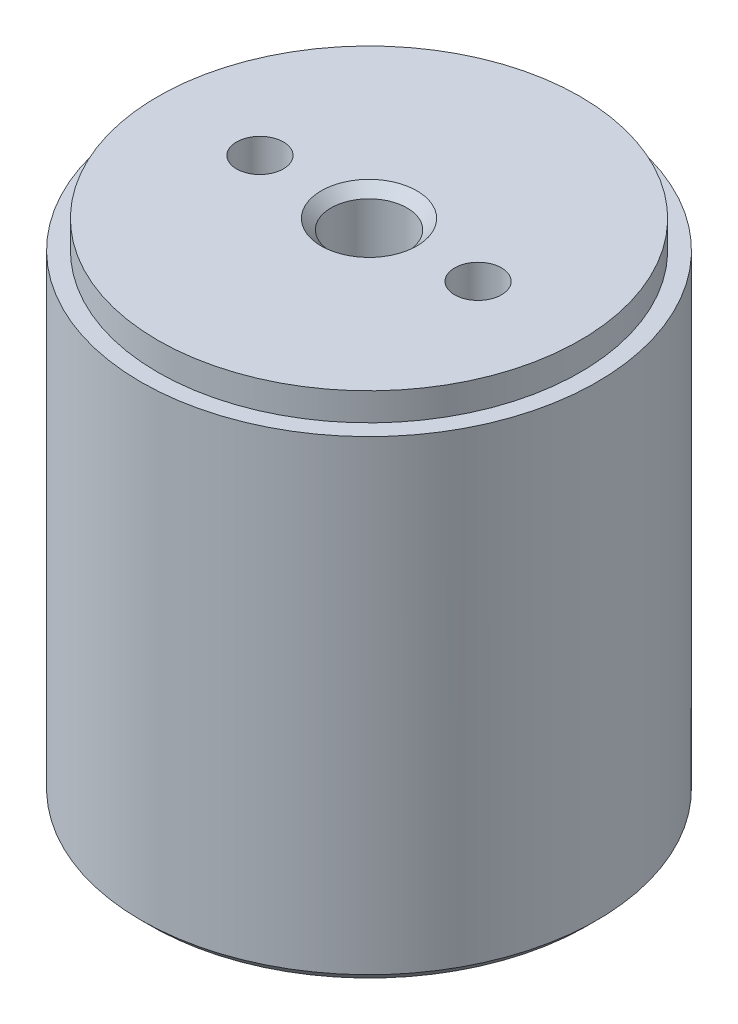
SolidWorks part; units mm, degrees
ref_plane "Front Plane" through (0, 0, 0) normal (0, 0, 1) x (1, 0, 0)
ref_plane "Top Plane" through (0, 0, 0) normal (0, 1, 0) x (1, 0, 0)
ref_plane "Right Plane" through (0, 0, 0) normal (1, 0, 0) x (0, 0, -1)
ref_plane "Plane1" through (0, 0, 0) normal (0, 0, -1) x (-1, 0, 0)
sketch "Sketch1" plane through (0, 0, 0) normal (0, 0, -1) x (-1, 0, 0)
  line L0 (-2.413, -4) -> (0, -4)
  line L1 (0, -4) -> (0, 24)
  line L2 (0, 24) -> (-11.5, 24)
  line L3 (-11.5, 24) -> (-11.5, 0)
  line L4 (-11.5, 0) -> (-8.8351, 0)
  line L5 (-7.4209, 0) -> (-3.6021, 0)
  line L6 (-2.413, -0.3246) -> (-2.413, -4)
  line L7 (0, -4) -> (0, 24) construction
  arc A0 (-8.8351, 0) -> (-7.4209, 0) centre (-8.128, 0.25) ccw
  arc A1 (-3.6021, 0) -> (-2.413, -0.3246) centre (-2.895, 0.25) ccw
revolve "Revolve1" add sketch "Sketch1" angle 360 about L7
sketch "Sketch2" plane through (0, 24, 0) normal (0, 1, 0) x (-1, 0, 0)
  circle A0 centre (0, 0) radius 10.65
extrude "Boss-Extrude1" add sketch "Sketch2" along normal blind 1.4
hole_wizard "M2 Clearance Hole1" positions "Sketch4" profile "Sketch3" hole size "M2" standard "ANSI Metric"
sketch "Sketch4" plane through (0, 0, 0) normal (0, -1, 0) x (-1, 0, 0)
  point P0 (-5.5, 0)
  point P1 (5.5, 0)
sketch "Sketch3" plane through (5.5, 0, 0) normal (1, 0, 0) x (0, 0, -1)
  line L0 (0, 0) -> (0, 5)
  line L1 (0, 5) -> (1.181, 5)
  line L2 (1.181, 5) -> (1.181, 0)
  line L5 (1.181, 0) -> (0, 0)
  line L10 (0, 5) -> (-1.181, 5) construction
  line L11 (0, -6.35) -> (0, 107.95) construction
  dimension "Hole Dia." = 2.362
  dimension "Hole Depth" = 5
  dimension "Drill Angle" = 180
hole_wizard "M2 Clearance Hole2" positions "Sketch6" profile "Sketch5" hole size "M2" standard "ANSI Metric"
sketch "Sketch6" plane through (0, -4, 0) normal (0, -1, 0) x (-1, 0, 0)
  point P0 (0, 0)
sketch "Sketch5" plane through (0, -4, 0) normal (1, 0, 0) x (0, 0, -1)
  line L0 (0, 0) -> (0, 9)
  line L1 (0, 9) -> (1.181, 9)
  line L2 (1.181, 9) -> (1.181, 0)
  line L5 (1.181, 0) -> (0, 0)
  line L10 (0, 9) -> (-1.181, 9) construction
  line L11 (0, -6.35) -> (0, 107.95) construction
  dimension "Hole Dia." = 2.362
  dimension "Hole Depth" = 9
  dimension "Drill Angle" = 180
hole_wizard "M3.5 Clearance Hole1" positions "Sketch8" profile "Sketch7" hole size "M3.5" standard "ANSI Metric"
sketch "Sketch8" plane through (0, 25.4, 0) normal (0, 1, 0) x (1, 0, 0)
  point P0 (0, 0)
sketch "Sketch7" plane through (0, 25.4, 0) normal (1, 0, 0) x (0, 0, 1)
  line L0 (0, 0) -> (0, 5)
  line L1 (0, 5) -> (1.915, 5)
  line L2 (1.915, 5) -> (1.915, 0)
  line L5 (1.915, 0) -> (0, 0)
  line L10 (0, 5) -> (-1.915, 5) construction
  line L11 (0, -6.35) -> (0, 107.95) construction
  dimension "Hole Dia." = 3.83
  dimension "Hole Depth" = 5
  dimension "Drill Angle" = 180
hole_wizard "M2 Clearance Hole3" positions "Sketch10" profile "Sketch9" hole size "M2" standard "ANSI Metric"
sketch "Sketch10" plane through (0, 25.4, 0) normal (0, 1, 0) x (1, 0, 0)
  point P0 (5.5, 0)
  point P1 (-5.5, 0)
sketch "Sketch9" plane through (5.5, 25.4, 0) normal (1, 0, 0) x (0, 0, 1)
  line L0 (0, 0) -> (0, 5)
  line L1 (0, 5) -> (1.181, 5)
  line L2 (1.181, 5) -> (1.181, 0)
  line L5 (1.181, 0) -> (0, 0)
  line L10 (0, 5) -> (-1.181, 5) construction
  line L11 (0, -6.35) -> (0, 107.95) construction
  dimension "Hole Dia." = 2.362
  dimension "Hole Depth" = 5
  dimension "Drill Angle" = 180
chamfer "Chamfer1" distance 0.498 angle 45 3 edges at (0, 0, 11.5) (0, -4, 2.413) (0, 25.4, 1.915)
